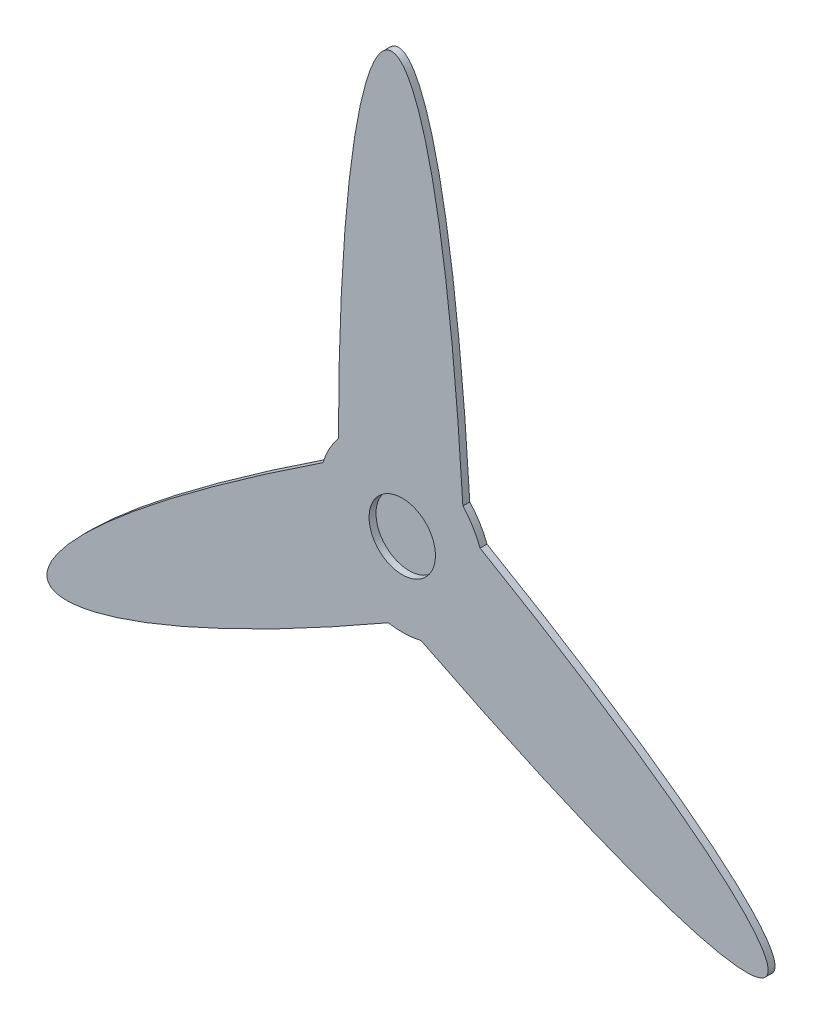
SolidWorks part; units mm, degrees
ref_plane "Front Plane" through (0, 0, 0) normal (0, 0, 1) x (1, 0, 0)
ref_plane "Top Plane" through (0, 0, 0) normal (0, 1, 0) x (1, 0, 0)
ref_plane "Right Plane" through (0, 0, 0) normal (1, 0, 0) x (0, 0, -1)
sketch "Sketch1" plane through (0, 0, 0) normal (0, 0, 1) x (1, 0, 0)
  line L0 (-8.9052, 298.6213) -> (0, 0) construction
  circle A0 centre (0, 0) radius 60
  circle A1 centre (0, 0) radius 28.5
  circle A2 centre (0, 0) radius 24
  circle A3 centre (0, 0) radius 300 construction
  arc A11 (262.9918, -141.9555) -> (260.7137, -146.0973) centre (260.2338, -143.1359) cw
  arc A12 (-256.8793, -152.7352) -> (-254.4315, -156.779) centre (-254.0748, -153.8003) ccw
  spline S0 degree 3 poles (43.837, 40.9672) (22.5733, 400.1357) (-45.6293, 373.0802) (-46.163, 38.3273) knots 0 0 0 0 1 1 1 1
  point P29 (0.001, 0)
  dimension "D1" = 120
  dimension "D2" = 57
  dimension "D3" = 48
  dimension "D4" = 600
  dimension "D5" = 90
  dimension "D6" = 45
extrude "Boss-Extrude2" add sketch "Sketch1" along normal blind 5
sketch "Sketch2" plane through (0, 0, 0) normal (0, 0, 1) x (1, 0, 0)
  line L0 (0, 28.5) -> (0, -28.5) construction
  line L1 (0, 28.5) -> (0, -28.5)
  arc A0 (0, 28.5) -> (0, -28.5) centre (0, 0) ccw
  dimension "D1" = 57
pattern_circular "CirPattern1" count 3 over 360 about axis through (0, 0, 5) along (0, 0, 1) of "Boss-Extrude2"
revolve "Revolve1" add sketch "Sketch2" angle 180 about L0
